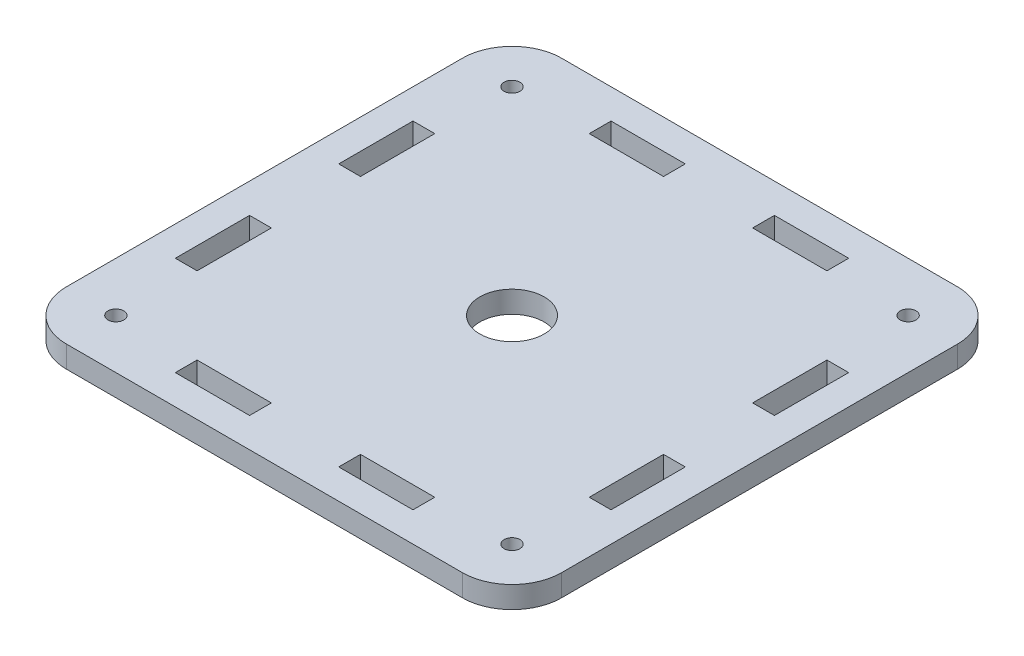
SolidWorks part; units mm, degrees
ref_plane "前视基准面" through (0, 0, 0) normal (0, 0, 1) x (1, 0, 0)
ref_plane "上视基准面" through (0, 0, 0) normal (0, 1, 0) x (1, 0, 0)
ref_plane "右视基准面" through (0, 0, 0) normal (1, 0, 0) x (0, 0, -1)
sketch "草图1" plane through (0, 0, 0) normal (0, 1, 0) x (1, 0, 0)
  line L1 (-50, -50) -> (50, -50)
  line L2 (-50, -50) -> (-50, 50)
  line L3 (-50, 50) -> (50, 50)
  line L4 (50, -50) -> (50, 50)
  line L5 (0, 50) -> (0, -50) construction
  line L6 (-50, 0) -> (50, 0) construction
  circle A0 centre (0, 0) radius 6.5
  point P0 (0, 0)
  dimension "D3" = 13
  dimension "D1" = 100
  dimension "D2" = 100
extrude "凸台-拉伸1" add sketch "草图1" along normal blind 4.4
fillet "圆角1" radius 10 4 edges at (50, 2.2, 50) (-50, 2.2, 50) (50, 2.2, -50) (-50, 2.2, -50)
sketch "草图2" plane through (0, 4.4, 0) normal (0, 1, 0) x (1, 0, 0)
  line L0 (0, 50) -> (0, 0) construction
  line L1 (40, 50) -> (-40, 50) construction
  line L2 (-24, 44) -> (-24, 39.6)
  line L3 (9, 44) -> (24, 44)
  line L4 (9, 44) -> (9, 39.6)
  line L5 (9, 39.6) -> (24, 39.6)
  line L6 (24, 44) -> (24, 39.6)
  line L7 (-9, 39.6) -> (-24, 39.6)
  line L8 (-9, 44) -> (-9, 39.6)
  line L9 (-9, 44) -> (-24, 44)
  line L10 (44, -9) -> (39.6, -9)
  line L11 (44, -9) -> (44, -24)
  line L12 (39.6, -9) -> (39.6, -24)
  line L13 (44, -24) -> (39.6, -24)
  line L14 (44, 9) -> (44, 24)
  line L15 (44, 24) -> (39.6, 24)
  line L16 (39.6, 9) -> (39.6, 24)
  line L17 (44, 9) -> (39.6, 9)
  line L18 (-9, -44) -> (-9, -39.6)
  line L19 (-9, -44) -> (-24, -44)
  line L20 (-9, -39.6) -> (-24, -39.6)
  line L21 (-24, -44) -> (-24, -39.6)
  line L22 (9, -44) -> (24, -44)
  line L23 (24, -44) -> (24, -39.6)
  line L24 (9, -39.6) -> (24, -39.6)
  line L25 (9, -44) -> (9, -39.6)
  line L26 (-44, 9) -> (-39.6, 9)
  line L27 (-44, 9) -> (-44, 24)
  line L28 (-39.6, 9) -> (-39.6, 24)
  line L29 (-44, 24) -> (-39.6, 24)
  line L30 (-44, -9) -> (-44, -24)
  line L31 (-44, -24) -> (-39.6, -24)
  line L32 (-39.6, -9) -> (-39.6, -24)
  line L33 (-44, -9) -> (-39.6, -9)
  circle A0 centre (40, 40) radius 1.6
  circle A1 centre (40, -40) radius 1.6
  circle A2 centre (-40, -40) radius 1.6
  circle A3 centre (-40, 40) radius 1.6
  point P40 (0, 0)
  point P50 (0, 0)
  dimension "D6" = 3.2
  dimension "D1" = 4.4
  dimension "D2" = 18
  dimension "D3" = 15
  dimension "D4" = 6
  dimension "D5" = 4
  dimension "D7" = 4
extrude "切除-拉伸1" cut sketch "草图2" against normal up to next
